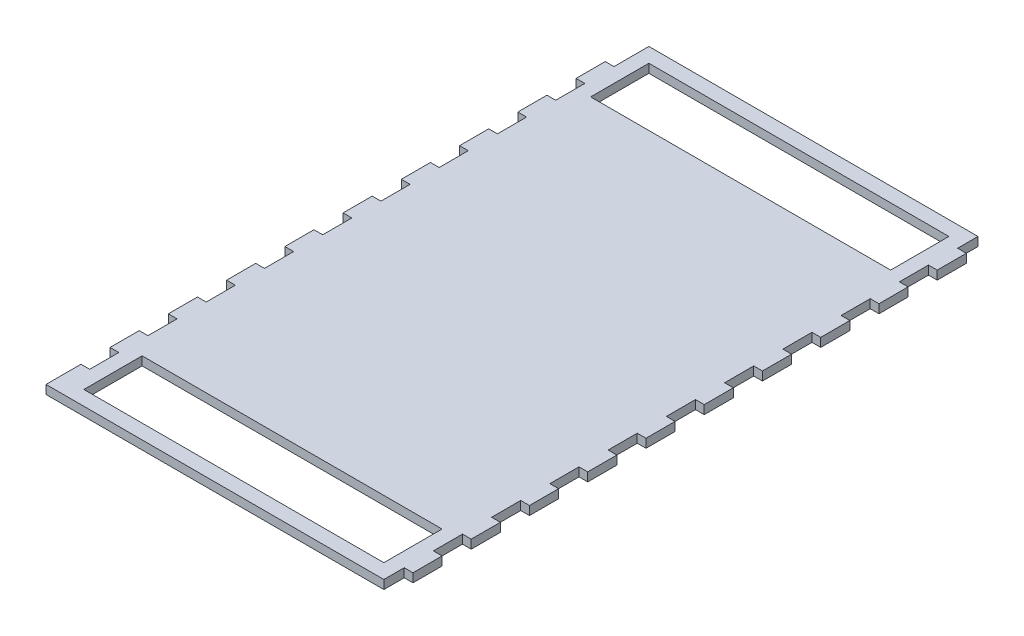
SolidWorks part; units mm, degrees
ref_plane "Front Plane" through (0, 0, 0) normal (0, 0, 1) x (1, 0, 0)
ref_plane "Top Plane" through (0, 0, 0) normal (0, 1, 0) x (1, 0, 0)
ref_plane "Right Plane" through (0, 0, 0) normal (1, 0, 0) x (0, 0, -1)
sketch "Sketch1" plane through (0, 0, 0) normal (0, 1, 0) x (1, 0, 0)
  line L1 (0, 0) -> (113, 0)
  line L2 (0, 0) -> (0, 204)
  line L3 (0, 204) -> (113, 204)
  line L4 (113, 0) -> (113, 204)
  dimension "D1" = 113
  dimension "D2" = 204
extrude "Boss-Extrude1" add sketch "Sketch1" along normal blind 3
sketch "Sketch2" plane through (113, 0, 0) normal (1, 0, 0) x (0, 0, -1)
  line L0 (0, 0) -> (204, 0) construction
  line L1 (7, 0) -> (17, 0)
  line L2 (7, 0) -> (7, 3)
  line L3 (7, 3) -> (17, 3)
  line L4 (17, 0) -> (17, 3)
  line L5 (0, 3) -> (204, 3) construction
  dimension "D1" = 10
  dimension "D2" = 7
extrude "Boss-Extrude2" add sketch "Sketch2" along normal blind 3 contours L1 L4 L3 L2
pattern_linear "LPattern1" count 10 spacing 20 along (0, 0, -1) of "Boss-Extrude2"
sketch "Sketch3" plane through (0, 0, 0) normal (-1, 0, 0) x (0, 0, 1)
  line L0 (-204, 3) -> (0, 3) construction
  line L5 (0, 0) -> (-12, 0)
  line L12 (0, 0) -> (0, 3)
  line L13 (0, 3) -> (-12, 3)
  line L14 (-12, 0) -> (-12, 3)
  line L15 (-204, 0) -> (0, 0) construction
  line L16 (-22, 0) -> (-32, 0)
  line L17 (-22, 0) -> (-22, 3)
  line L18 (-22, 3) -> (-32, 3)
  line L19 (-32, 0) -> (-32, 3)
  line L20 (-42, 0) -> (-42, 3)
  line L21 (-42, 0) -> (-52, 0)
  line L22 (-52, 0) -> (-52, 3)
  line L23 (-42, 3) -> (-52, 3)
  line L24 (-62, 0) -> (-62, 3)
  line L25 (-62, 0) -> (-72, 0)
  line L26 (-72, 0) -> (-72, 3)
  line L27 (-62, 3) -> (-72, 3)
  line L28 (-82, 0) -> (-82, 3)
  line L29 (-82, 0) -> (-92, 0)
  line L30 (-92, 0) -> (-92, 3)
  line L31 (-82, 3) -> (-92, 3)
  line L32 (-102, 0) -> (-102, 3)
  line L33 (-102, 0) -> (-112, 0)
  line L34 (-112, 0) -> (-112, 3)
  line L35 (-102, 3) -> (-112, 3)
  line L36 (-122, 0) -> (-122, 3)
  line L37 (-122, 0) -> (-132, 0)
  line L38 (-132, 0) -> (-132, 3)
  line L39 (-122, 3) -> (-132, 3)
  line L40 (-142, 0) -> (-142, 3)
  line L41 (-142, 0) -> (-152, 0)
  line L42 (-152, 0) -> (-152, 3)
  line L43 (-142, 3) -> (-152, 3)
  line L44 (-162, 0) -> (-162, 3)
  line L45 (-162, 0) -> (-172, 0)
  line L46 (-172, 0) -> (-172, 3)
  line L47 (-162, 3) -> (-172, 3)
  line L48 (-182, 0) -> (-182, 3)
  line L49 (-182, 0) -> (-192, 0)
  line L50 (-192, 0) -> (-192, 3)
  line L51 (-182, 3) -> (-192, 3)
  point P12 (-12, 1.5)
  dimension "D1" = 12
  dimension "D2" = 10
  dimension "D3" = 10
  dimension "D4" = 9
sketch "Sketch4" plane through (0, 3, 0) normal (0, 1, 0) x (1, 0, 0)
  line L0 (113, 204) -> (0, 204) construction
  line L2 (0, 0) -> (113, 0) construction
  line L5 (113, 19.575) -> (113, 29.575) construction
  line L6 (108, 25) -> (5, 25)
  line L7 (108, 25) -> (108, 5)
  line L8 (108, 5) -> (5, 5)
  line L9 (5, 25) -> (5, 5)
  line L10 (0, 29.575) -> (0, 19.575) construction
  line L11 (108, 199) -> (5, 199)
  line L12 (5, 179) -> (5, 199)
  line L13 (108, 179) -> (5, 179)
  line L14 (108, 179) -> (108, 199)
  dimension "D1" = 5
  dimension "D2" = 5
  dimension "D3" = 5
  dimension "D4" = 20
  dimension "D5" = 5
extrude "Cut-Extrude1" cut sketch "Sketch4" against normal through all
extrude "Boss-Extrude3" add sketch "Sketch3" along normal blind 3
